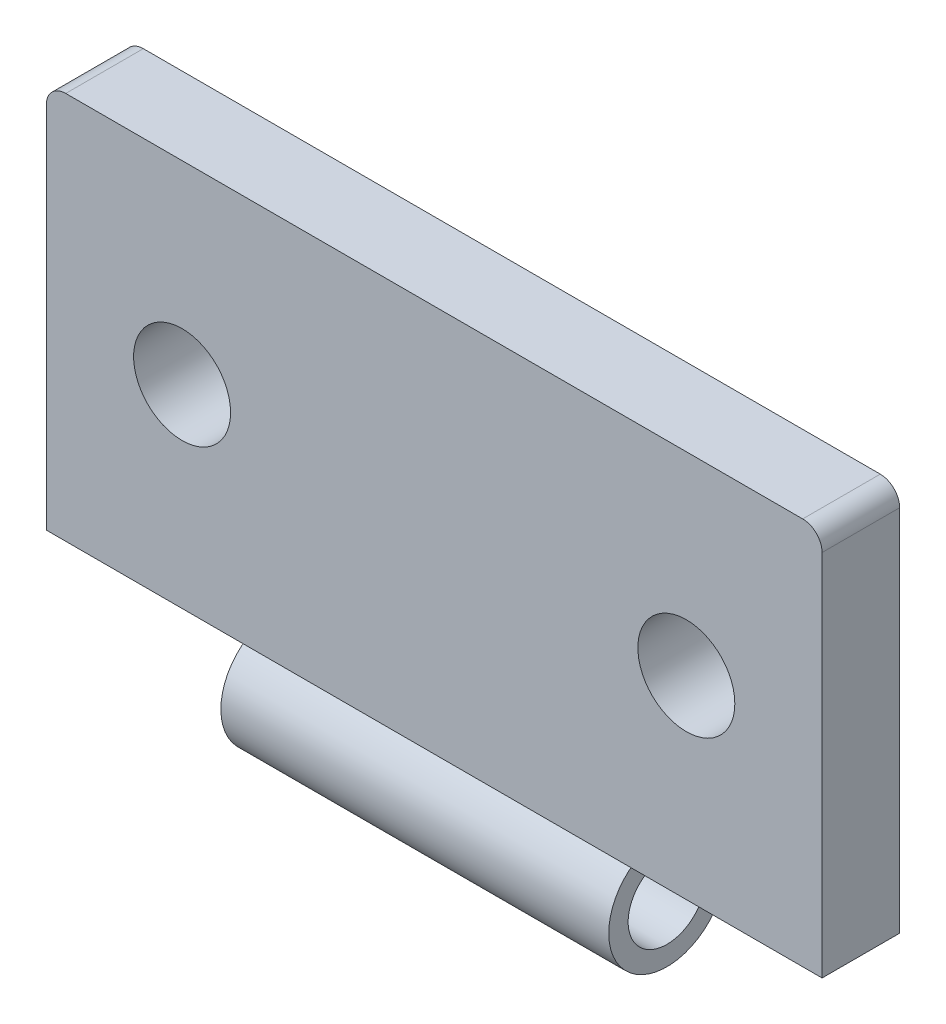
SolidWorks part; units mm, degrees
ref_plane "Front Plane" through (0, 0, 0) normal (0, 0, 1) x (1, 0, 0)
ref_plane "Top Plane" through (0, 0, 0) normal (0, 1, 0) x (1, 0, 0)
ref_plane "Right Plane" through (0, 0, 0) normal (1, 0, 0) x (0, 0, -1)
sketch "Sketch2" plane through (0, 0, 0) normal (0, 0, 1) x (1, 0, 0)
  line L1 (-20, 10) -> (20, 10)
  line L2 (-20, 10) -> (-20, -10)
  line L3 (-20, -10) -> (20, -10)
  line L4 (20, 10) -> (20, -10)
  line L5 (-20, 10) -> (20, -10) construction
  line L6 (-20, -10) -> (20, 10) construction
  circle A0 centre (-13, 0) radius 2.5
  circle A1 centre (13, 0) radius 2.5
  point P0 (0, 0)
  dimension "D3" = 5
  dimension "D1" = 40
  dimension "D2" = 20
  dimension "D4" = 7
  dimension "D5" = 7
extrude "Boss-Extrude2" add sketch "Sketch2" along normal mid plane 4
sketch "Sketch5" plane through (0, 0, 0) normal (1, 0, 0) x (0, 0, -1)
  circle A0 centre (0, -12.5) radius 3
  circle A1 centre (0, -12.5) radius 2
  dimension "D1" = 6
  dimension "D2" = 4
  dimension "D3" = 12.5
extrude "Boss-Extrude3" add sketch "Sketch5" along normal mid plane 20
fillet "Fillet1" radius 1 2 edges at (20, 10, 0) (-20, 10, 0)
